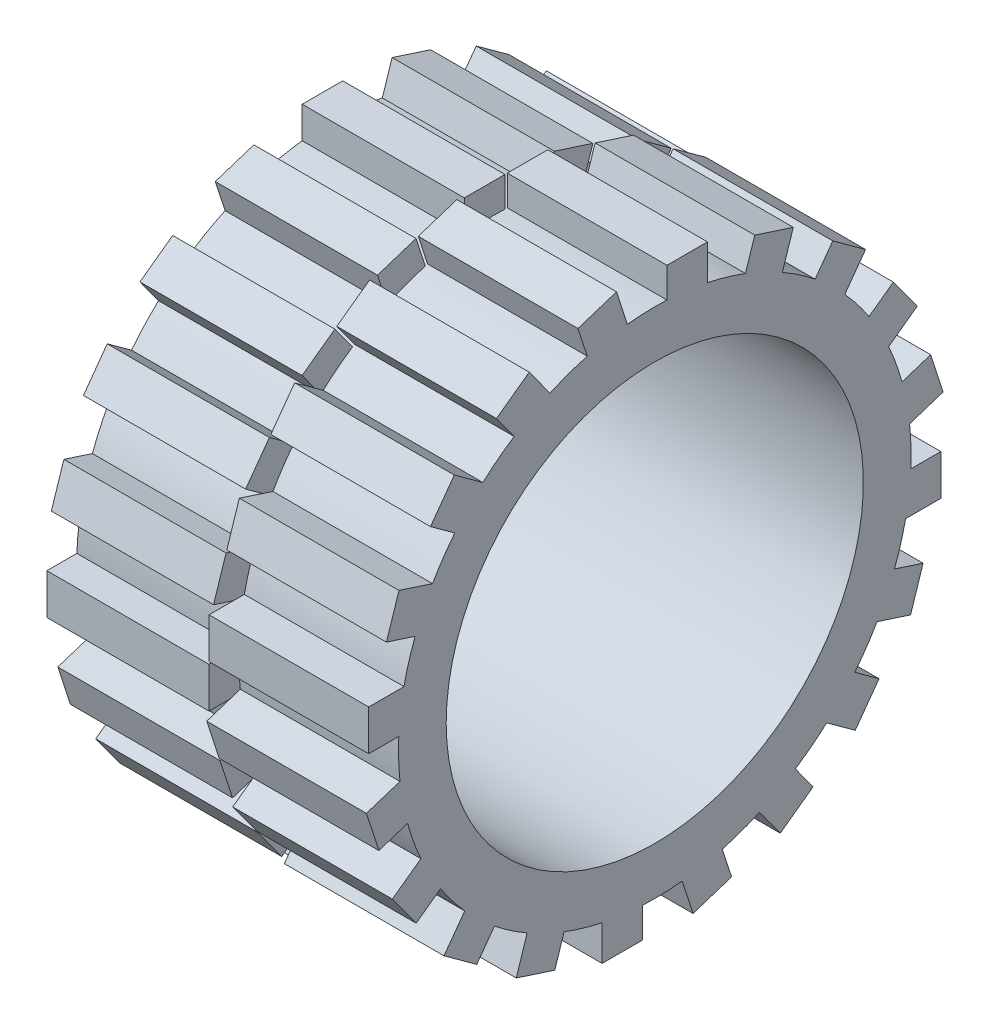
SolidWorks part; units mm, degrees
ref_plane "Front Plane" through (0, 0, 0) normal (0, 0, 1) x (1, 0, 0)
ref_plane "Top Plane" through (0, 0, 0) normal (0, 1, 0) x (1, 0, 0)
ref_plane "Right Plane" through (0, 0, 0) normal (1, 0, 0) x (0, 0, -1)
sketch "Sketch1" plane through (0, 0, 0) normal (1, 0, 0) x (0, 0, -1)
  circle A0 centre (0, 0) radius 10.75
  circle A1 centre (0, 0) radius 8.75
  dimension "D1" = 21.5
  dimension "D2" = 17.5
extrude "Boss-Extrude1" add sketch "Sketch1" along normal blind 13.5 contours A0
sketch "Sketch2" plane through (0, 0, 0) normal (-1, 0, 0) x (0, 0, 1)
  circle A0 centre (0, 0) radius 8.75
  dimension "D1" = 17.5
extrude "Cut-Extrude1" cut sketch "Sketch2" against normal through all
ref_plane "Plane1" through (0, 0, 10) normal (0, 0, 1) x (1, 0, 0)
sketch "Sketch3" plane through (0, 0, 10) normal (0, 0, 1) x (1, 0, 0)
  line L0 (0, 0.4108) -> (0, -1.2892)
  line L1 (0, 10.75) -> (0, -10.75) construction
  line L2 (0, -1.2892) -> (50000, -1.2892) construction
  line L3 (6.8029, -10.75) -> (6.8029, 10.75) construction
  line L6 (0, 0.4108) -> (6.8029, 0.4108)
  line L7 (6.8029, 0.4108) -> (6.8029, -1.2892)
  line L8 (6.8029, -1.2892) -> (0, -1.2892)
  line L12 (6.8029, 0.4108) -> (6.8029, 0.5104) construction
  line L13 (13.5, -10.75) -> (13.5, 10.75) construction
  line L14 (6.8029, 0.5104) -> (13.5, 0.5104)
  line L15 (6.8029, 0.5104) -> (6.8029, 2.2104)
  line L16 (6.8029, 2.2104) -> (13.5, 2.2104)
  line L17 (13.5, 0.5104) -> (13.5, 2.2104)
  dimension "D1" = 1.7
  dimension "D2" = 1.7
extrude "Boss-Extrude2" add sketch "Sketch3" along normal blind 2 contours L6 L7 L8 L0 | L15 L14 L17 L16
pattern_circular "CirPattern1" count 21 every 18 about axis through (0, 0, 0) along (1, 0, 0) of "Boss-Extrude2"
sketch "Sketch5" plane through (0, 0, 0) normal (-1, 0, 0) x (0, 0, 1)
  text T0 "Group 69" font "Century Gothic" height 0.9
extrude "Cut-Extrude5" cut sketch "Sketch5" against normal blind 5
